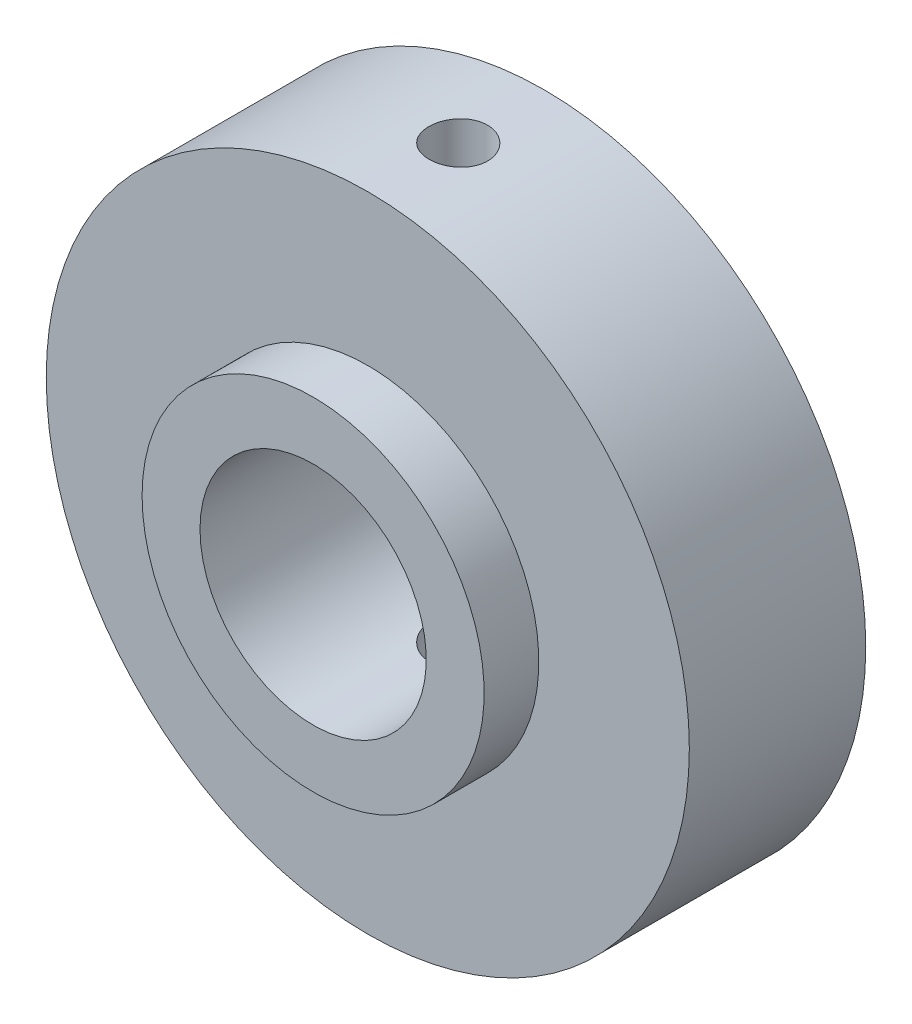
SolidWorks part; units mm, degrees
ref_plane "Front Plane" through (0, 0, 0) normal (0, 0, 1) x (1, 0, 0)
ref_plane "Top Plane" through (0, 0, 0) normal (0, 1, 0) x (1, 0, 0)
ref_plane "Right Plane" through (0, 0, 0) normal (1, 0, 0) x (0, 0, -1)
sketch "Sketch1" plane through (0, 0, 0) normal (0, 1, 0) x (1, 0, 0)
  line L0 (2.2794, 19.1299) -> (2.2794, -20.4608) construction
  line L1 (-1.9206, -12.1554) -> (-4.0706, -12.1554)
  line L2 (-1.9206, -12.1554) -> (-1.9206, -3.5734)
  line L3 (-1.9206, -3.5734) -> (-4.0706, -3.5734)
  line L4 (-4.0706, -12.1554) -> (-4.0706, -3.5734)
  line L6 (-4.0706, -3.5734) -> (-4.0706, 7.5178)
  line L7 (-4.0706, -12.1554) -> (-9.6586, -12.1554)
  line L8 (-4.0706, -12.1554) -> (-4.0706, -5.6054)
  line L9 (-4.0706, -5.6054) -> (-9.6586, -5.6054)
  line L10 (-9.6586, -12.1554) -> (-9.6586, -5.6054)
  line L11 (-1.9206, -12.1554) -> (-4.0706, -12.1554)
  line L12 (-1.9206, -12.1554) -> (-5.1079, -12.1554)
  line L13 (-1.9206, -12.1554) -> (-4.0706, -12.1554)
  line L14 (-4.0706, -12.1554) -> (-1.9206, -12.1554)
  line L15 (-1.9206, -12.1554) -> (-4.0706, -12.1554)
  line L16 (-1.9206, -12.1554) -> (-1.9206, -14.1854)
  line L17 (-1.9206, -14.1854) -> (-4.0706, -14.1854)
  line L18 (-4.0706, -12.1554) -> (-4.0706, -14.1854)
  dimension "D1" = 4.2
  dimension "D2" = 6.35
  dimension "D3" = 5.588
  dimension "D4" = 2.032
  dimension "D5" = 6.55
  dimension "D6" = 2.03
  dimension "D7" = 2.03
  dimension "D8" = 6.35
revolve "Revolve1" add sketch "Sketch1" angle 360 about L0
ref_plane "Plane1" through (0, 11.938, 0) normal (0, 1, 0) x (1, 0, 0)
sketch "Sketch2" plane through (0, 11.938, 0) normal (0, 1, 0) x (1, 0, 0)
  line L0 (2.3692, -12.5173) -> (2.3692, -5.2557) construction
  line L1 (-4.8469, -8.8865) -> (11.4377, -8.8865) construction
  circle A0 centre (2.3692, -8.8865) radius 1.0922
  dimension "D1" = 2.1844
extrude "Cut-Extrude1" cut sketch "Sketch2" against normal through all
